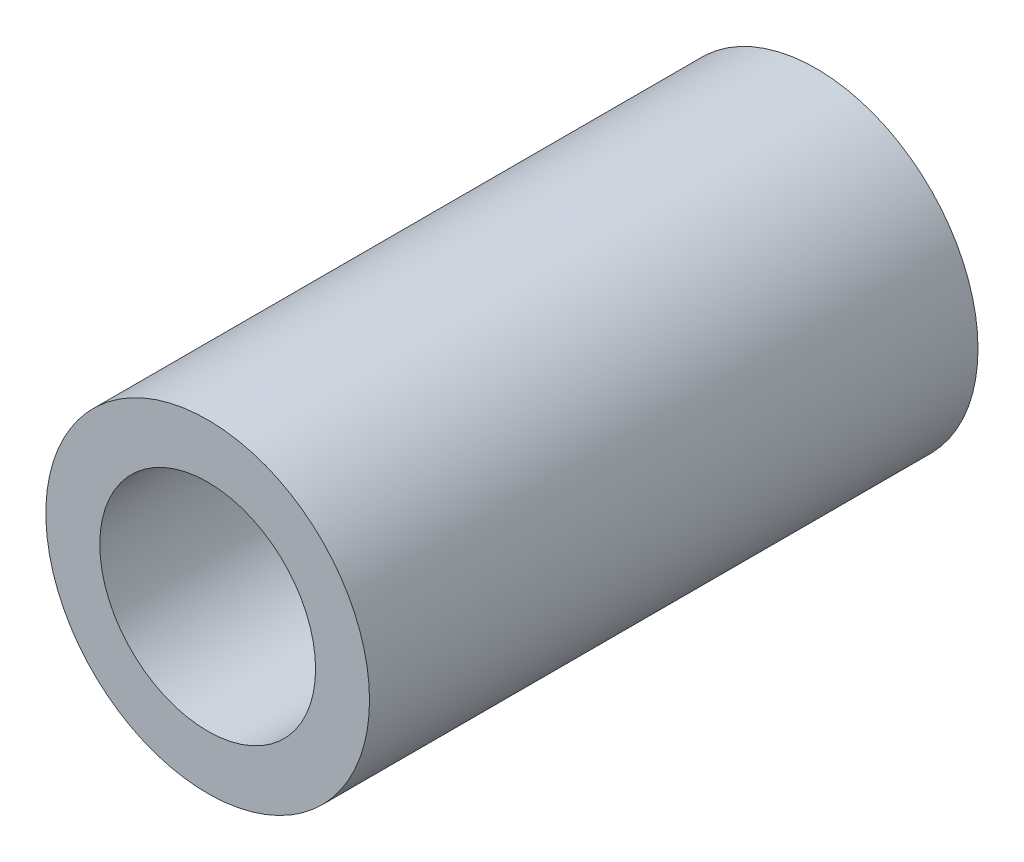
SolidWorks part; units mm, degrees
ref_plane "Front" through (0, 0, 0) normal (0, 0, 1) x (1, 0, 0)
ref_plane "Top" through (0, 0, 0) normal (0, 1, 0) x (1, 0, 0)
ref_plane "Right" through (0, 0, 0) normal (1, 0, 0) x (0, 0, -1)
sketch "Sketch1" plane through (0, 0, 0) normal (0, 0, 1) x (1, 0, 0)
  circle A0 centre (0, 0) radius 12.7
  circle A1 centre (0, 0) radius 19.05
  dimension "D1" = 25.4
  dimension "D2" = 6.35
extrude "Boss-Extrude1" add sketch "Sketch1" along normal blind 71.628
